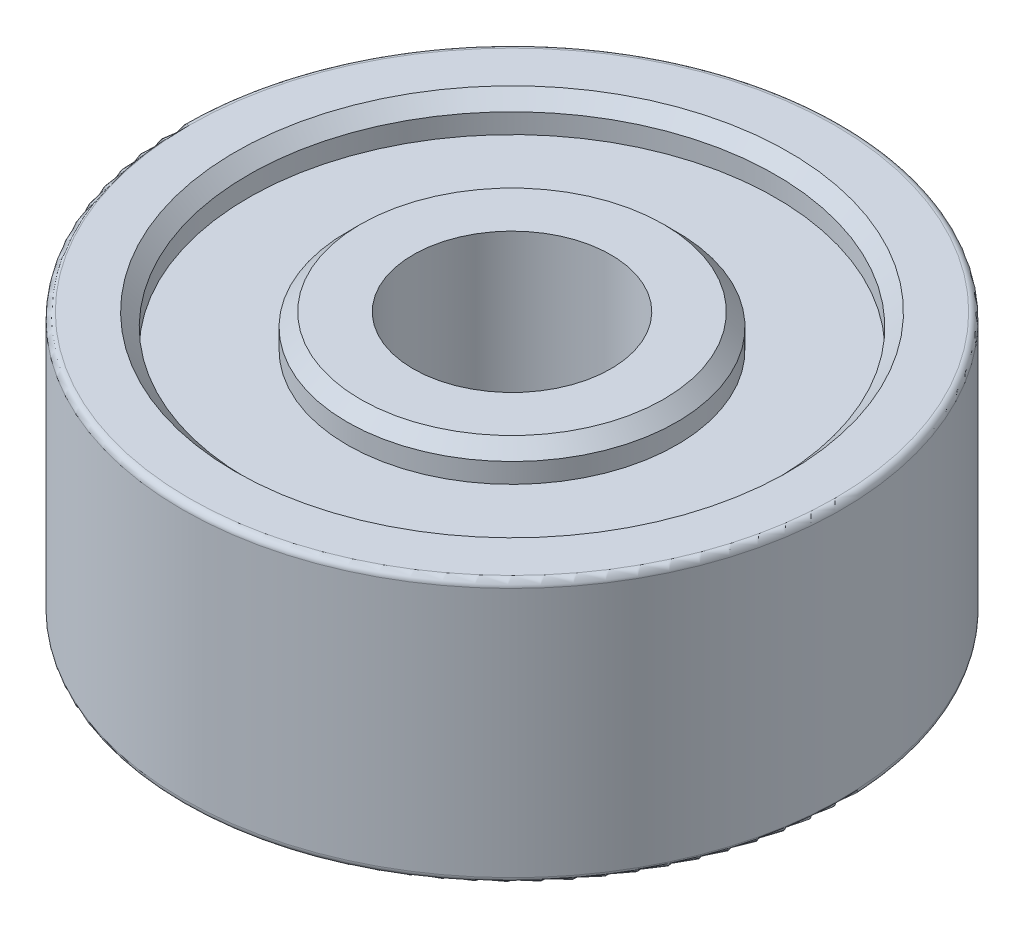
SolidWorks part; units mm, degrees
material "Plain Carbon Steel"
ref_plane "Front Plane" through (0, 0, 0) normal (0, 0, 1) x (1, 0, 0)
ref_plane "Top Plane" through (0, 0, 0) normal (0, 1, 0) x (1, 0, 0)
ref_plane "Right Plane" through (0, 0, 0) normal (1, 0, 0) x (0, 0, -1)
sketch "Sketch2" plane through (0, 0, 0) normal (0, 1, 0) x (1, 0, 0)
  circle A0 centre (0, 0) radius 5
  circle A1 centre (0, 0) radius 1.5
  dimension "D1" = 10
  dimension "D2" = 3
extrude "Boss-Extrude1" add sketch "Sketch2" along normal mid plane 4
sketch "Sketch3" plane through (0, 2, 0) normal (0, 1, 0) x (1, 0, 0)
  circle A0 centre (0, 0) radius 2.5
  circle A1 centre (0, 0) radius 4
  circle A2 centre (0, 0) radius 1.5 construction
  dimension "D1" = 1
  dimension "D2" = 1.5
extrude "Cut-Extrude1" cut sketch "Sketch3" against normal blind 0.5
mirror "Mirror1" about plane through (0, 0, 0) normal (0, 1, 0) of "Cut-Extrude1"
chamfer "Chamfer1" distance 0.2 angle 45 4 edges at (0, 2, 2.5) (0, 2, 4) (0, -2, 4) (0, -2, 2.5)
fillet "Fillet1" radius 0.1 2 edges at (0, -2, 5) (0, 2, 5)
